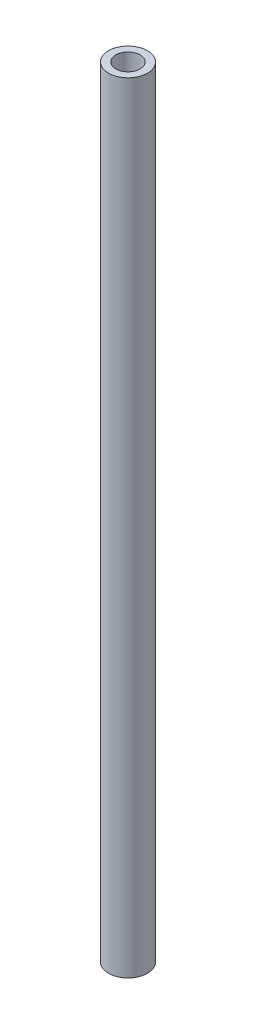
SolidWorks part; units mm, degrees
material "PVC Rigid"
ref_plane "Front Plane" through (0, 0, 0) normal (0, 0, 1) x (1, 0, 0)
ref_plane "Top Plane" through (0, 0, 0) normal (0, 1, 0) x (1, 0, 0)
ref_plane "Right Plane" through (0, 0, 0) normal (1, 0, 0) x (0, 0, -1)
sketch "Sketch1" plane through (0, 0, 0) normal (0, 1, 0) x (1, 0, 0)
  circle A0 centre (0, 0) radius 12.7
  circle A1 centre (0, 0) radius 7.9375
extrude "Boss-Extrude1" add sketch "Sketch1" along normal blind 508
